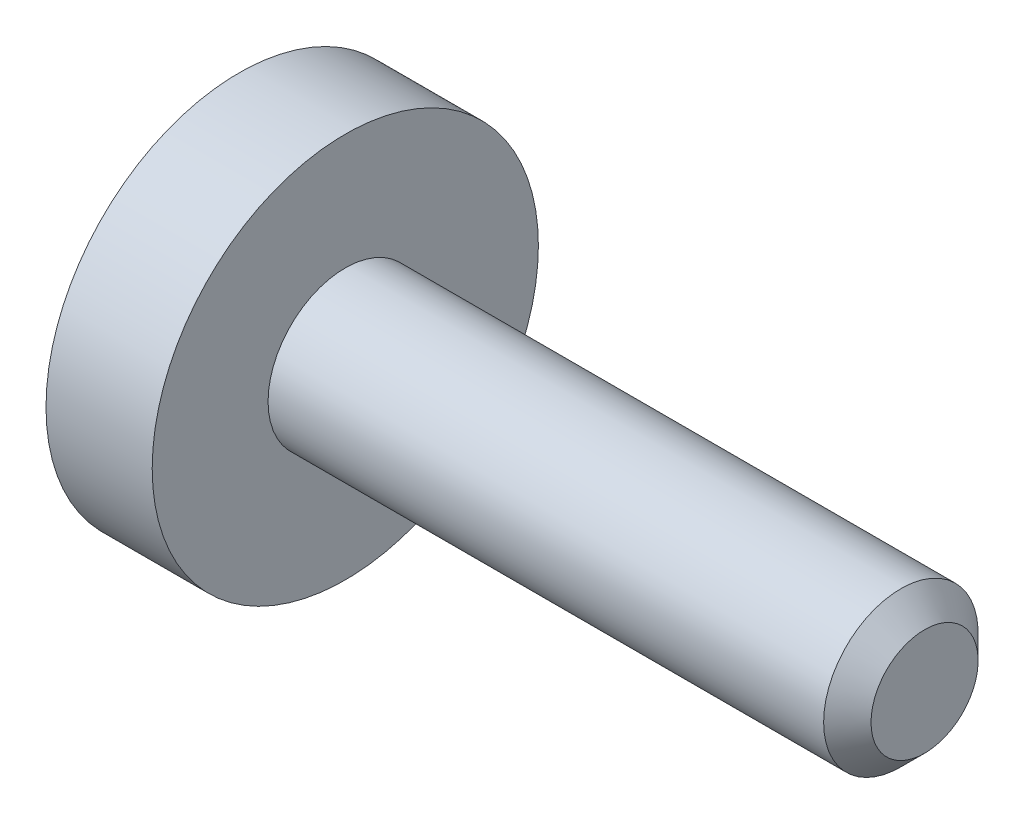
SolidWorks part; units mm, degrees
material "AISI 304"
ref_plane "正面" through (0, 0, 0) normal (0, 0, 1) x (1, 0, 0)
ref_plane "平面" through (0, 0, 0) normal (0, 1, 0) x (1, 0, 0)
ref_plane "右側面" through (0, 0, 0) normal (1, 0, 0) x (0, 0, -1)
ref_plane "Plane1" through (0, 0, 0) normal (0, 0, 1) x (1, 0, 0)
sketch "Sketch1" plane through (0, 0, 0) normal (0, 0, 1) x (1, 0, 0)
  line L0 (-1.1, 0) -> (-1.1, 2)
  line L1 (-1.1, 2) -> (0, 2)
  line L2 (0, 2) -> (0, 0.8)
  line L3 (0, 0.8) -> (5.7545, 0.8)
  line L4 (5.7545, 0.8) -> (6, 0.5545)
  line L5 (6, 0.5545) -> (6, 0)
  line L6 (6, 0) -> (-1.1, 0)
  line L7 (6, 0) -> (-1.1, 0) construction
  dimension "D1" = 0.8
revolve "Revolve1" add sketch "Sketch1" angle 360 about L7
cosmetic thread "Cosmetic Thread1" parameters "D1"=5.5748, "D2"=1.509
ref_plane "Plane2" through (-1.1, 0, 0) normal (1, 0, 0) x (0, 0, -1)
sketch "Sketch2" plane through (-1.1, 0, 0) normal (1, 0, 0) x (0, 0, -1)
  line L0 (-0.65, -0.3753) -> (0, -0.7506)
  line L1 (0, -0.7506) -> (0.65, -0.3753)
  line L2 (0.65, -0.3753) -> (0.65, 0.3753)
  line L3 (0.65, 0.3753) -> (0, 0.7506)
  line L4 (0, 0.7506) -> (-0.65, 0.3753)
  line L5 (-0.65, 0.3753) -> (-0.65, -0.3753)
extrude "Cut-Extrude1" cut sketch "Sketch2" along normal blind 1.2
